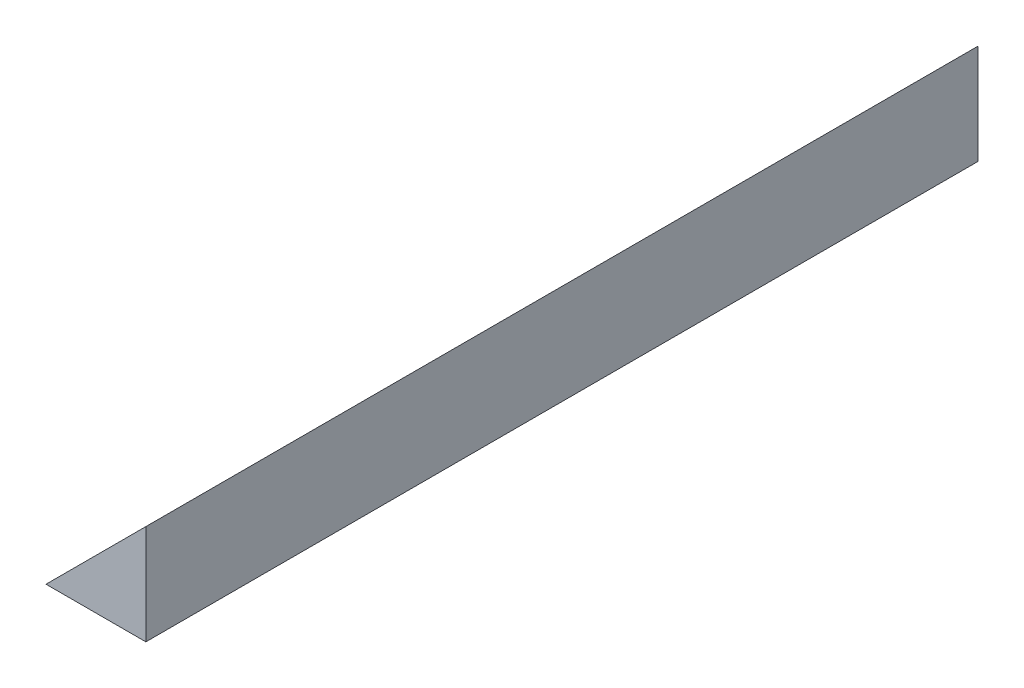
SolidWorks part; units mm, degrees
ref_plane "Спереди" through (0, 0, 0) normal (0, 0, 1) x (1, 0, 0)
ref_plane "Сверху" through (0, 0, 0) normal (0, 1, 0) x (1, 0, 0)
ref_plane "Слева" through (0, 0, 0) normal (1, 0, 0) x (0, 0, -1)
sketch "Эскиз1" plane through (0, 0, 0) normal (0, 0, 1) x (1, 0, 0)
  line L0 (-6, 0) -> (0, 0)
  line L1 (0, 0) -> (0, 6)
  line L2 (0, 6) -> (-6, 0)
  dimension "D1" = 6
extrude "Вытянуть1" add sketch "Эскиз1" along normal blind 50
